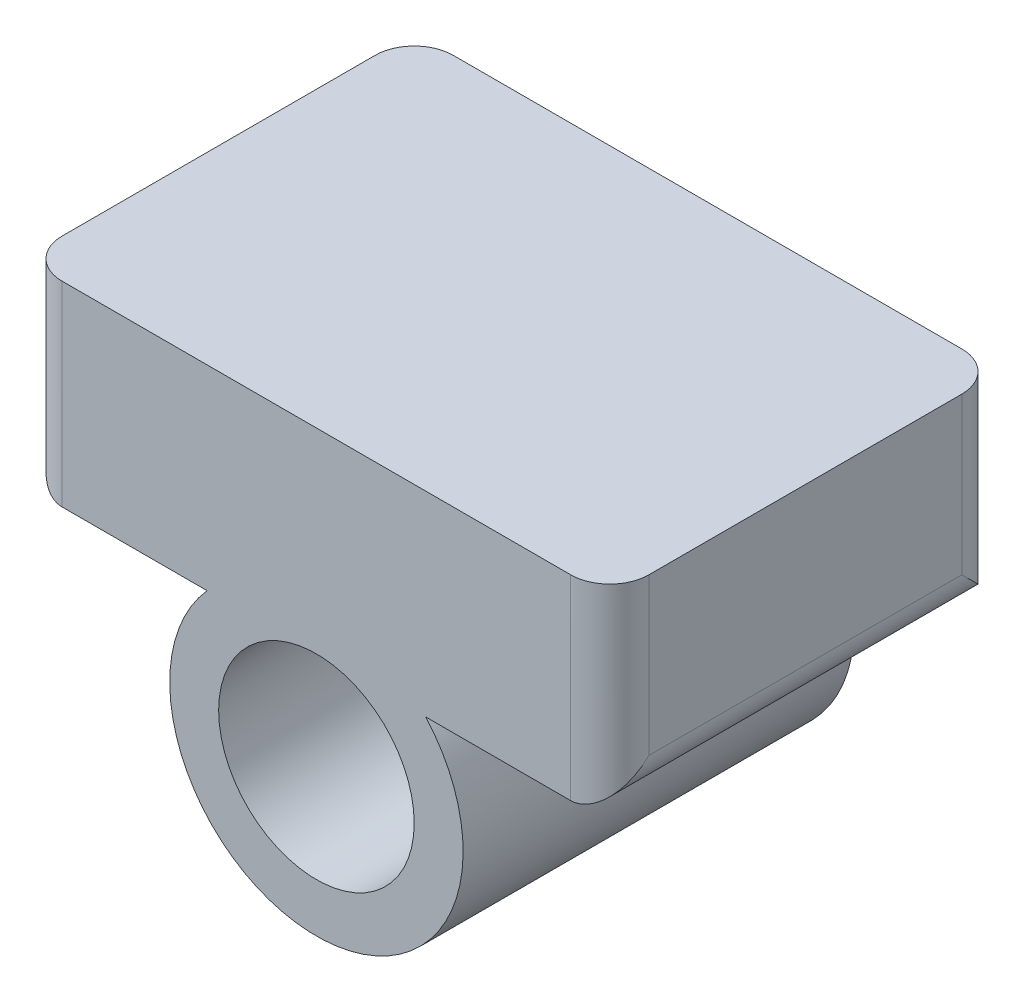
SolidWorks part; units mm, degrees
ref_plane "Front Plane" through (0, 0, 0) normal (0, 0, 1) x (1, 0, 0)
ref_plane "Top Plane" through (0, 0, 0) normal (0, 1, 0) x (1, 0, 0)
ref_plane "Right Plane" through (0, 0, 0) normal (1, 0, 0) x (0, 0, -1)
sketch "Sketch1" plane through (0, 0, 0) normal (0, 0, 1) x (1, 0, 0)
  line L1 (15, 5) -> (-15, 5)
  line L2 (15, 5) -> (15, 15)
  line L3 (15, 15) -> (-15, 15)
  line L4 (-15, 5) -> (-15, 15)
  circle A0 centre (0, 0) radius 5
  circle A1 centre (0, 0) radius 7.5
  point P8 (0, 5)
  dimension "D1" = 10
  dimension "D2" = 15
  dimension "D3" = 10
  dimension "D4" = 30
extrude "Boss-Extrude1" add sketch "Sketch1" along normal blind 20 contours A1 L1 L2 L3 L4 | L1 A1 A0 | L1 A1
fillet "Fillet1" radius 2 6 edges at (15, 5, 10) (-15, 5, 10) (-15, 10, 20) (-15, 10, 0) (15, 10, 0) (15, 10, 20)
